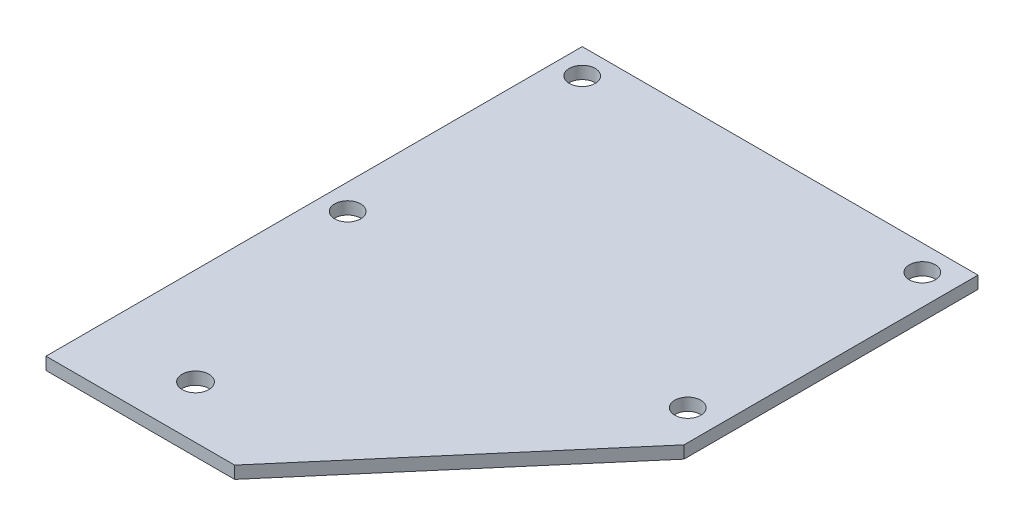
SolidWorks part; units mm, degrees
ref_plane "Front Plane" through (0, 0, 0) normal (0, 0, 1) x (1, 0, 0)
ref_plane "Top Plane" through (0, 0, 0) normal (0, 1, 0) x (1, 0, 0)
ref_plane "Right Plane" through (0, 0, 0) normal (1, 0, 0) x (0, 0, -1)
sketch "Sketch1" plane through (0, 0, 0) normal (0, 1, 0) x (1, 0, 0)
  line L0 (0, -68.58) -> (0, 68.58)
  line L1 (0, 68.58) -> (101.24, 68.58)
  line L2 (101.24, 68.58) -> (101.24, -6.62)
  line L3 (101.24, -6.62) -> (48.26, -68.58)
  line L4 (48.26, -68.58) -> (0, -68.58)
  line L5 (0, 62.08) -> (101.24, 62.08) construction
  line L6 (0, 2.08) -> (101.24, 2.08) construction
  line L7 (6.5, 62.08) -> (6.5, 2.08) construction
  line L8 (93.5, 62.08) -> (93.5, 2.08) construction
  line L9 (0, -55.16) -> (59.735, -55.16) construction
  circle A0 centre (93.5, 62.08) radius 3.33
  circle A1 centre (6.5, 62.08) radius 3.33
  circle A2 centre (93.5, 2.08) radius 3.33
  circle A3 centre (6.5, 2.08) radius 3.33
  circle A4 centre (24.82, -55.16) radius 3.42
  point P4 (0, 0)
  point P24 (21.4, -55.16)
  point P25 (24.82, -58.58)
  dimension "D1" = 6.66
  dimension "D10" = 6.84
  dimension "D2" = 101.24
  dimension "D3" = 75.2
  dimension "D4" = 48.26
  dimension "D5" = 137.16
  dimension "D6" = 87
  dimension "D7" = 60
  dimension "D8" = 6.5
  dimension "D9" = 6.5
  dimension "D11" = 10
  dimension "D12" = 21.4
extrude "Boss-Extrude1" add sketch "Sketch1" along normal blind 3.175
